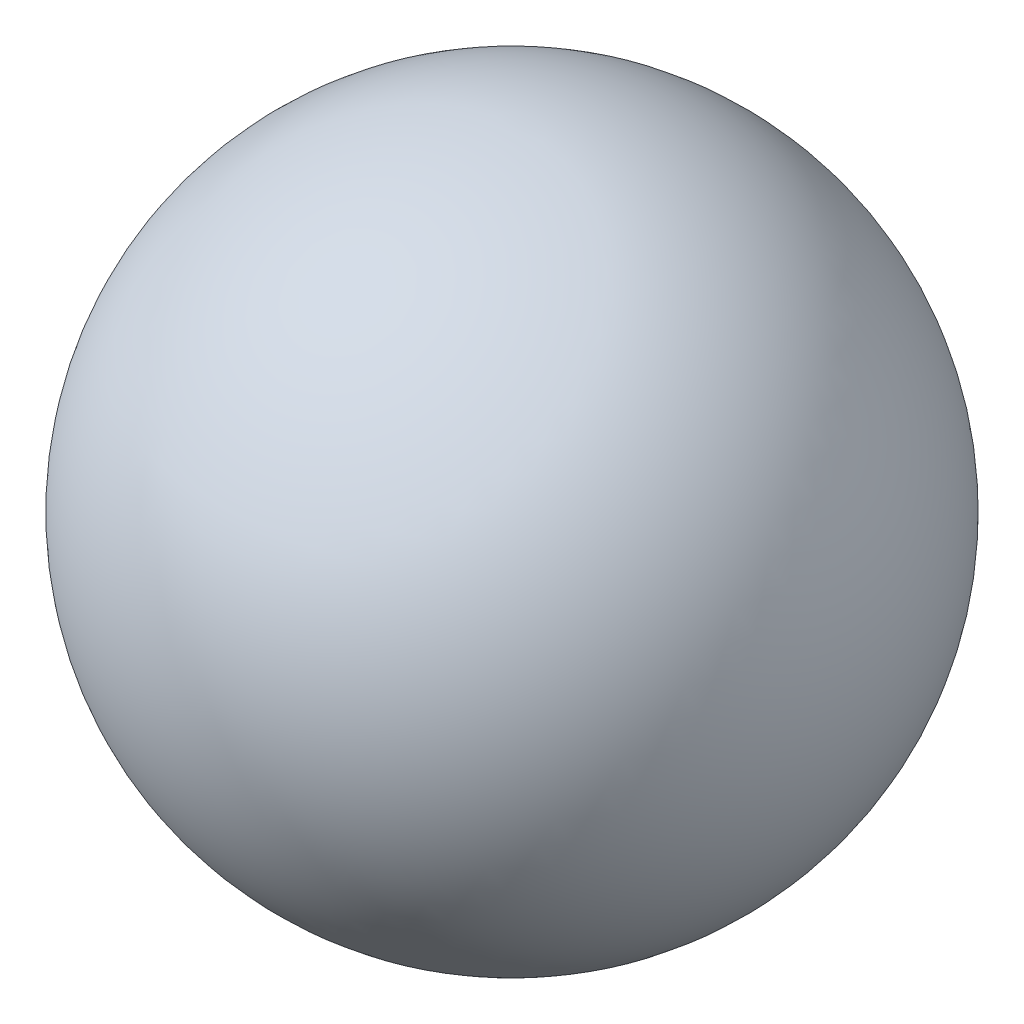
SolidWorks part; units mm, degrees
ref_plane "Front Plane" through (0, 0, 0) normal (0, 0, 1) x (1, 0, 0)
ref_plane "Top Plane" through (0, 0, 0) normal (0, 1, 0) x (1, 0, 0)
ref_plane "Right Plane" through (0, 0, 0) normal (1, 0, 0) x (0, 0, -1)
sketch "Sketch1" plane through (0, 0, 0) normal (0, 0, 1) x (1, 0, 0)
  line L0 (0, 0) -> (0, 127)
  circle A0 centre (0, 0) radius 127
  dimension "D1" = 254
revolve "Revolve1" add sketch "Sketch1" angle 360 about L0
